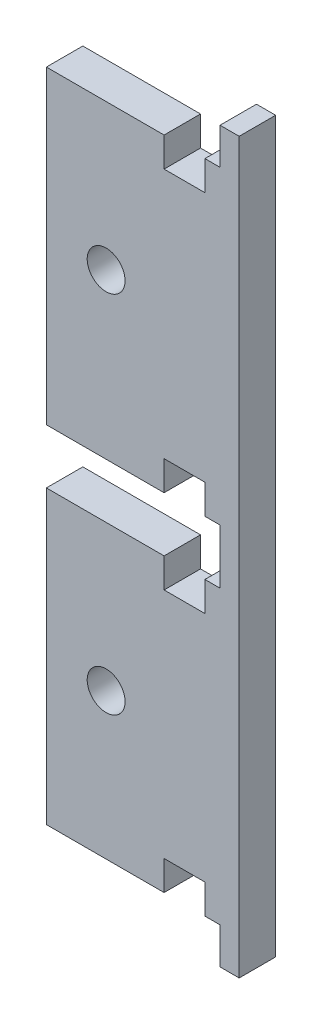
SolidWorks part; units mm, degrees
material "AISI 4130 Steel, annealed at 865C"
ref_plane "X-Y Datum" through (0, 0, 0) normal (0, 0, 1) x (1, 0, 0)
ref_plane "X-Z Datum" through (0, 0, 0) normal (0, 1, 0) x (1, 0, 0)
ref_plane "Y-Z Datum" through (0, 0, 0) normal (1, 0, 0) x (0, 0, -1)
sketch "Sketch2" plane through (0, 0, 0) normal (0, 0, 1) x (1, 0, 0)
  line L0 (34.925, 127) -> (0, 127) construction
  line L1 (0, 0) -> (40.64, 0)
  line L2 (0, 0) -> (0, 127)
  line L3 (0, 127) -> (40.64, 127)
  line L4 (40.64, 0) -> (40.64, 127)
  point P7 (17.4625, 31.75)
  point P8 (17.4625, 95.25)
  dimension "D1" = 40.64
extrude "Boss-Extrude1" add sketch "Sketch2" along normal blind 6.35
hole_wizard "M6 Clearance Hole1" positions "Sketch3" profile "Sketch4" hole size "M6" standard "ANSI Metric" end condition through all
sketch "Sketch3" plane through (0, 0, 6.35) normal (0, 0, 1) x (1, 0, 0)
  point P0 (17.4625, 31.75)
  point P3 (17.4625, 95.25)
sketch "Sketch4" plane through (17.4625, 31.75, 6.35) normal (1, 0, 0) x (0, -1, 0)
  line L0 (0, 0) -> (0, 6.35)
  line L1 (0, 6.35) -> (3.3, 6.35)
  line L2 (3.3, 6.35) -> (3.3, 0)
  line L5 (3.3, 0) -> (0, 0)
  line L11 (0, -6.35) -> (0, 107.95) construction
  dimension "Thru Hole Dia." = 6.6
  dimension "Thru Hole Depth" = 6.35
sketch "Sketch5" plane through (0, 0, 6.35) normal (0, 0, 1) x (1, 0, 0)
  line L0 (7.0505, 127) -> (7.0505, 0)
  line L1 (40.64, 127) -> (0, 127) construction
  line L2 (0, 0) -> (40.64, 0) construction
  circle A0 centre (17.4625, 95.25) radius 3.3 construction
  point P6 (14.1625, 95.25)
  line M4 (0, 127) -> (0, 0)
  line M5 (0, 0) -> (40.64, 0)
  line M7 (40.64, 127) -> (0, 127)
  dimension "D1" = 7.112
extrude "Cut-Extrude1" cut sketch "Sketch5" against normal through all and the other way through all contours L0 M7 M4 M5
sketch "Sketch6" plane through (0, 0, 6.35) normal (0, 0, 1) x (1, 0, 0)
  line L0 (-3.175, 120.65) -> (38.1, 120.65)
  line L1 (38.1, 120.65) -> (38.1, 130.175)
  line L2 (38.1, 130.175) -> (-3.175, 130.175)
  line L3 (-3.175, 130.175) -> (-3.175, 120.65)
  line L4 (0, 123.825) -> (34.925, 123.825)
  line L5 (34.925, 123.825) -> (34.925, 127)
  line L6 (34.925, 127) -> (0, 127)
  line L7 (0, 127) -> (0, 123.825)
  line L8 (0, 123.825) -> (34.925, 123.825)
  line L9 (34.925, 123.825) -> (34.925, 127)
  line L10 (34.925, 127) -> (0, 127)
  line L11 (0, 127) -> (0, 123.825)
  line L12 (0, 60.325) -> (34.925, 60.325)
  line L13 (34.925, 60.325) -> (34.925, 63.5)
  line L14 (34.925, 63.5) -> (0, 63.5)
  line L15 (0, 63.5) -> (0, 60.325)
  line L16 (0, 60.325) -> (34.925, 60.325)
  line L17 (34.925, 60.325) -> (34.925, 63.5)
  line L18 (34.925, 63.5) -> (0, 63.5)
  line L19 (0, 63.5) -> (0, 60.325)
  line L24 (0, 0) -> (34.925, 0)
  line L25 (34.925, 0) -> (34.925, 3.175)
  line L26 (34.925, 3.175) -> (0, 3.175)
  line L27 (0, 3.175) -> (0, 0)
  line L28 (38.1, 66.675) -> (-3.175, 66.675)
  line L29 (-3.175, 66.675) -> (-3.175, 57.15)
  line L30 (-3.175, 57.15) -> (38.1, 57.15)
  line L31 (38.1, 57.15) -> (38.1, 66.675)
  line L32 (38.1, 6.35) -> (-3.175, 6.35)
  line L33 (-3.175, 6.35) -> (-3.175, -3.175)
  line L34 (-3.175, -3.175) -> (38.1, -3.175)
  line L35 (38.1, -3.175) -> (38.1, 6.35)
  line L36 (37.3063, 127) -> (37.3063, 0)
  line L37 (40.64, 127) -> (7.0505, 127) construction
  line L38 (7.0505, 0) -> (40.64, 0) construction
  line M19 (7.0505, 127) -> (7.0505, 0)
  line M20 (7.0505, 0) -> (40.64, 0)
  line M22 (40.64, 127) -> (7.0505, 127)
  dimension "D5" = 2.3813
  dimension "D1" = 0
  dimension "D2" = 0
  dimension "D4" = 3.175
extrude "Cut-Extrude2" cut sketch "Sketch6" against normal through all contours L36 L9 L8 L0 M22 M19 | L8 L9 M22 M19 | L36 L28 L18 L17 L16 L30 M19 | L17 L18 L16 M19 | L36 L32 L26 L25 M19 M20 | L25 L26 M19 M20
sketch "Sketch7" plane through (0, 0, 6.35) normal (0, 0, 1) x (1, 0, 0)
  line L0 (34.671, 115.5065) -> (27.559, 115.5065)
  line L5 (27.559, 121.031) -> (27.559, 115.5065)
  line L18 (34.29, 120.65) -> (27.94, 120.65)
  line L19 (34.29, 120.65) -> (34.29, 115.8875)
  line L20 (34.29, 115.8875) -> (27.94, 115.8875)
  line L21 (27.94, 120.65) -> (27.94, 115.8875)
  line L22 (34.29, 71.4375) -> (27.94, 71.4375)
  line L23 (34.29, 71.4375) -> (34.29, 66.675)
  line L24 (34.29, 66.675) -> (27.94, 66.675)
  line L25 (27.94, 71.4375) -> (27.94, 66.675)
  line L26 (34.29, 57.15) -> (27.94, 57.15)
  line L27 (34.29, 57.15) -> (34.29, 52.3875)
  line L28 (34.29, 52.3875) -> (27.94, 52.3875)
  line L29 (27.94, 57.15) -> (27.94, 52.3875)
  line L30 (34.29, 11.1125) -> (27.94, 11.1125)
  line L31 (34.29, 11.1125) -> (34.29, 6.35)
  line L32 (34.29, 6.35) -> (27.94, 6.35)
  line L33 (27.94, 11.1125) -> (27.94, 6.35)
  line L34 (34.671, 121.031) -> (27.559, 121.031)
  line L35 (34.671, 121.031) -> (34.671, 115.5065)
  line L36 (34.671, 66.294) -> (27.559, 66.294)
  line L37 (27.559, 71.8185) -> (27.559, 66.294)
  line L38 (34.671, 71.8185) -> (27.559, 71.8185)
  line L39 (34.671, 71.8185) -> (34.671, 66.294)
  line L40 (34.671, 52.0065) -> (27.559, 52.0065)
  line L41 (27.559, 57.531) -> (27.559, 52.0065)
  line L42 (34.671, 57.531) -> (27.559, 57.531)
  line L43 (34.671, 57.531) -> (34.671, 52.0065)
  line L44 (34.671, 5.969) -> (27.559, 5.969)
  line L45 (27.559, 11.4935) -> (27.559, 5.969)
  line L46 (34.671, 11.4935) -> (27.559, 11.4935)
  line L47 (34.671, 11.4935) -> (34.671, 5.969)
  point P40 (0, 0)
  point P41 (0, 0)
  line M4 (37.3063, 120.65) -> (7.0505, 120.65)
  line M6 (7.0505, 66.675) -> (37.3063, 66.675)
  line M8 (37.3063, 57.15) -> (7.0505, 57.15)
  line M10 (7.0505, 6.35) -> (37.3063, 6.35)
  dimension "D1" = 0.381
extrude "Cut-Extrude3" cut sketch "Sketch7" against normal through all contours L30 L33 L31 M10 | L47 L46 L45 L33 L30 L31 M10 | L47 L45 L44 M10 | L29 L28 L27 M8 | L43 L27 L28 L29 L41 L40 M8 | L43 L42 L41 M8 | L39 L37 L36 M6 | L22 L25 L23 M6 | L39 L38 L37 L25 L22 L23 M6 | L21 L20 L19 M4 | L35 L19 L20 L21 L5 L0 M4 | L35 L34 L5 M4
